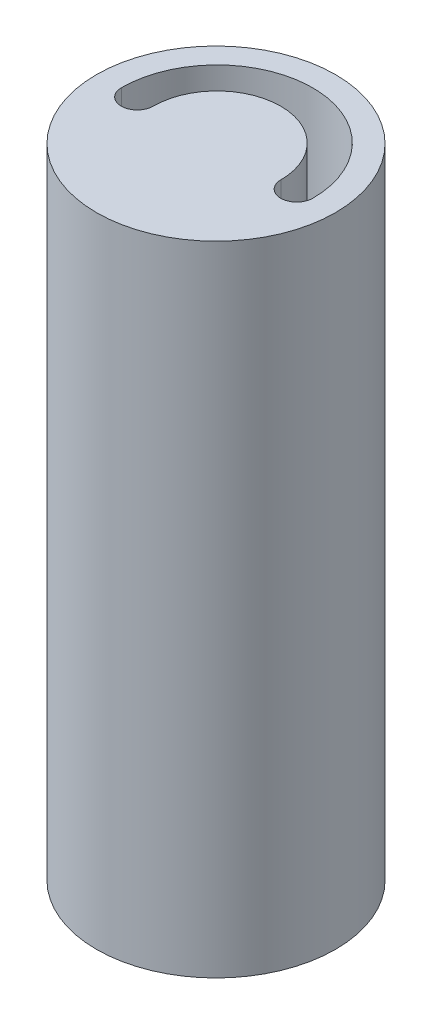
SolidWorks part; units mm, degrees
ref_plane "Front Plane" through (0, 0, 0) normal (0, 0, 1) x (1, 0, 0)
ref_plane "Top Plane" through (0, 0, 0) normal (0, 1, 0) x (1, 0, 0)
ref_plane "Right Plane" through (0, 0, 0) normal (1, 0, 0) x (0, 0, -1)
sketch "Sketch1" plane through (0, 0, 0) normal (0, 0, 1) x (1, 0, 0)
  circle A0 centre (0, 0) radius 28.1
extrude "Boss-Extrude2" add sketch "Sketch1" along normal blind 61.3
sketch "Sketch3" plane through (0, 0, 61.3) normal (0, 0, 1) x (1, 0, 0)
  circle A1 centre (0, -7) radius 18.6
extrude "Cut-Extrude2" cut sketch "Sketch3" against normal blind 58.8 contours A1
sketch "Sketch4" plane through (0, 0, 0) normal (0, 0, -1) x (-1, 0, 0)
  line L1 (-28.1, -28.1) -> (28.1, -28.1)
  line L2 (-28.1, -28.1) -> (-28.1, 28.1)
  line L3 (-28.1, 28.1) -> (28.1, 28.1)
  line L4 (28.1, -28.1) -> (28.1, 28.1)
  line L5 (-28.1, -28.1) -> (28.1, 28.1) construction
  line L6 (-28.1, 28.1) -> (28.1, -28.1) construction
  point P0 (0, 0)
extrude "Boss-Extrude3" add sketch "Sketch4" along normal blind 56.2
sketch "Sketch5" plane through (0, 0, 2.5) normal (0, 0, 1) x (1, 0, 0)
  circle A1 centre (0, -7) radius 16.1
extrude "Cut-Extrude4" cut sketch "Sketch5" against normal blind 5
sketch "Sketch6" plane through (0, 0, -56.2) normal (0, 0, -1) x (-1, 0, 0)
  line L1 (-24.8987, -24.8896) -> (24.8987, -24.8896)
  line L2 (-24.8987, -24.8896) -> (-24.8987, 24.8896)
  line L3 (-24.8987, 24.8896) -> (24.8987, 24.8896)
  line L4 (24.8987, -24.8896) -> (24.8987, 24.8896)
  line L5 (-24.8987, -24.8896) -> (24.8987, 24.8896) construction
  line L6 (-24.8987, 24.8896) -> (24.8987, -24.8896) construction
  point P0 (0, 0)
extrude "Cut-Extrude5" cut sketch "Sketch6" against normal blind 53.7
sketch "Sketch7" plane through (0, -28.1, 0) normal (0, -1, 0) x (-1, 0, 0)
  circle A0 centre (0, 28.1) radius 28.1
extrude "Boss-Extrude4" add sketch "Sketch7" along normal blind 321.5 contours A0
sketch "Sketch8" plane through (0, -349.6, 0) normal (0, -1, 0) x (-1, 0, 0)
  line L1 (-1.6583, 25.8321) -> (1.6583, 25.8321)
  line L3 (-1.6583, 30.8321) -> (1.6583, 30.8321)
  arc A2 (-1.6583, 30.8321) -> (-1.6583, 25.8321) centre (0, 28.3321) ccw
  arc A3 (1.6583, 25.8321) -> (1.6583, 30.8321) centre (0, 28.3321) ccw
extrude "Cut-Extrude6" cut sketch "Sketch8" against normal blind 10
sketch "Sketch9" plane through (0, -349.6, 0) normal (0, -1, 0) x (-1, 0, 0)
  circle A1 centre (0, 28.3321) radius 3
extrude "Cut-Extrude7" cut sketch "Sketch9" against normal blind 1
sketch "Sketch10" plane through (0, -349.6, 0) normal (0, -1, 0) x (-1, 0, 0)
  circle A1 centre (0, 28.3321) radius 6.025
extrude "Cut-Extrude8" cut sketch "Sketch10" against normal blind 0.1
sketch "Sketch15" plane through (0, -349.6, 0) normal (0, -1, 0) x (-1, 0, 0)
  line L0 (6.025, 28.3321) -> (-6.025, 28.3321)
  circle A0 centre (0, 28.3321) radius 6.025 construction
  arc A1 (15, 28.3321) -> (-15, 28.3321) centre (0, 28.3321) ccw
sketch3d "3DSketch2"
  line L1 (-15, -349.6, -28.3321) -> (-22.5, -349.6, -28.3321)
  line L2 (-15, -349.6, -28.3321) -> (-15, -20, -28.3321)
  line L3 (-15, -20, -28.3321) -> (-22.5, -20, -28.3321)
  line L4 (-22.5, -349.6, -28.3321) -> (-22.5, -20, -28.3321)
sweep "Cut-Sweep4" cut profiles "3DSketch2" path "Sketch15"
sketch "Sketch18" plane through (0, 0, 61.3) normal (0, 0, 1) x (1, 0, 0)
  circle A1 centre (0, 18.75) radius 3.75
extrude "Cut-Extrude9" cut sketch "Sketch18" against normal blind 100
sketch "Sketch19" plane through (0, -349.6, 0) normal (0, -1, 0) x (-1, 0, 0)
  circle A0 centre (-18.75, 28.3321) radius 3.75
  circle A1 centre (18.75, 28.3321) radius 3.75
extrude "Cut-Extrude11" cut sketch "Sketch19" against normal blind 325
sketch "Sketch20" plane through (0, 0, -56.2) normal (0, 0, -1) x (-1, 0, 0)
  line L1 (-28.1, -28.1) -> (28.1, -28.1)
  line L2 (-28.1, -28.1) -> (-28.1, 28.1)
  line L3 (-28.1, 28.1) -> (28.1, 28.1)
  line L4 (28.1, -28.1) -> (28.1, 28.1)
extrude "Cut-Extrude13" cut sketch "Sketch20" against normal blind 200
sketch "Sketch21" plane through (0, -28.1, 0) normal (0, 1, 0) x (1, 0, 0)
  circle A1 centre (0, 28.1) radius 28.1
sketch "Sketch22" plane through (0, -349.6, 0) normal (0, -1, 0) x (-1, 0, 0)
  circle A0 centre (0, 28.3321) radius 28.3321
extrude "Cut-Extrude15" cut sketch "Sketch22" against normal blind 171.5
